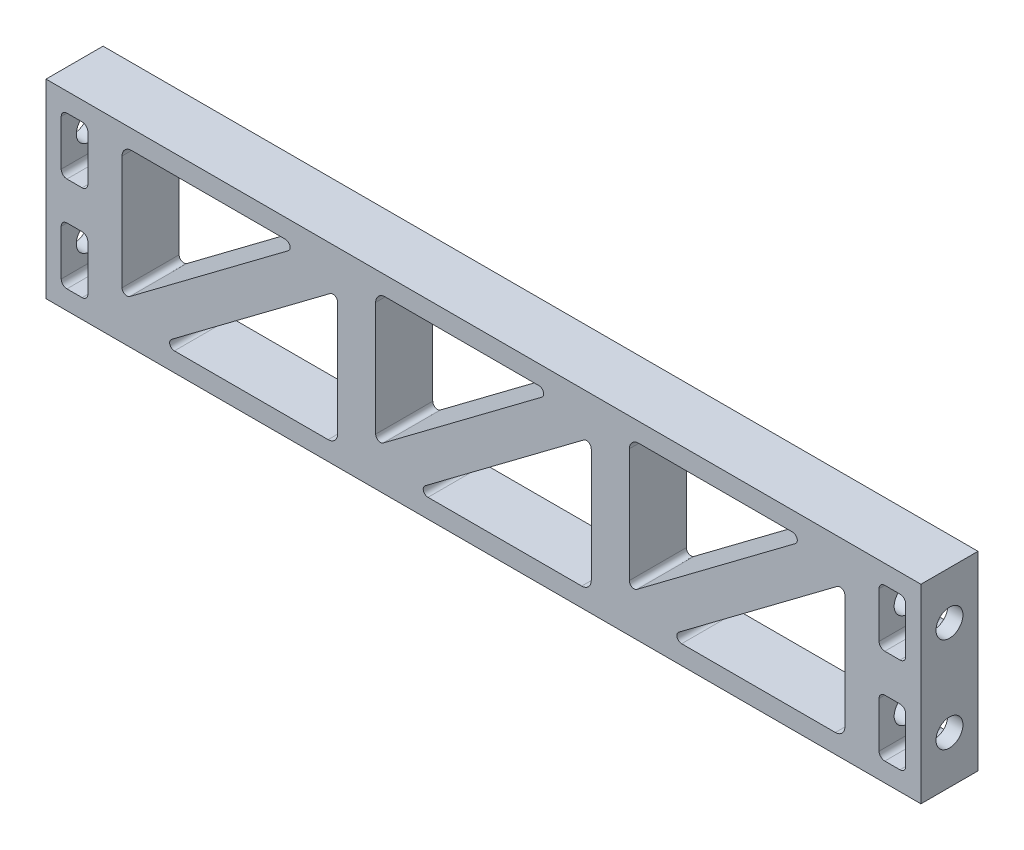
SolidWorks part; units mm, degrees
material "PE High Density"
ref_plane "Front Plane" through (0, 0, 0) normal (0, 0, 1) x (1, 0, 0)
ref_plane "Top Plane" through (0, 0, 0) normal (0, 1, 0) x (1, 0, 0)
ref_plane "Right Plane" through (0, 0, 0) normal (1, 0, 0) x (0, 0, -1)
sketch "Sketch1" plane through (0, 0, 0) normal (0, 0, 1) x (1, 0, 0)
  line L0 (-24.3417, 15.875) -> (-24.3417, -15.875) construction
  line L1 (-73.025, 15.875) -> (73.025, 15.875)
  line L2 (-73.025, 15.875) -> (-73.025, -15.875)
  line L3 (-73.025, -15.875) -> (73.025, -15.875)
  line L4 (73.025, 15.875) -> (73.025, -15.875)
  line L5 (-73.025, 15.875) -> (73.025, -15.875) construction
  line L6 (-73.025, -15.875) -> (73.025, 15.875) construction
  line L7 (24.3417, 15.875) -> (24.3417, -15.875) construction
  line L9 (-69.85, -12.7) -> (-27.5167, 12.7) construction
  line L10 (-69.85, -12.7) -> (-69.85, 12.7) construction
  line L11 (-64.3071, -11.2256) -> (-29.9209, 9.4061)
  line L12 (-73.025, -15.875) -> (-24.3417, -15.875)
  line L13 (-73.025, -15.875) -> (-73.025, 15.875)
  line L14 (-73.025, 15.875) -> (-24.3417, 15.875)
  line L15 (-24.3417, -15.875) -> (-24.3417, 15.875) construction
  line L16 (-69.85, 12.7) -> (-27.5167, 12.7) construction
  line L17 (-27.5167, -12.7) -> (-27.5167, 12.7) construction
  line L18 (-69.85, -12.7) -> (-27.5167, -12.7) construction
  line L19 (-67.4457, -9.4061) -> (-33.0595, 11.2256)
  line L20 (-69.0332, -14.0613) -> (-26.6999, 11.3387) construction
  line L21 (-69.85, -8.0448) -> (-69.85, 11.1125)
  line L22 (-70.6668, -11.3387) -> (-28.3334, 14.0613) construction
  line L23 (-68.2625, 12.7) -> (-33.4679, 12.7)
  line L24 (-63.8988, -12.7) -> (-29.1042, -12.7)
  line L25 (-27.5167, -11.1125) -> (-27.5167, 8.0448)
  line L26 (-15.6238, -11.2256) -> (18.7624, 9.4061)
  line L27 (-18.7624, -9.4061) -> (15.6238, 11.2256)
  line L28 (-21.1667, -8.0448) -> (-21.1667, 11.1125)
  line L29 (-19.5792, 12.7) -> (15.2154, 12.7)
  line L30 (-15.2154, -12.7) -> (19.5792, -12.7)
  line L31 (21.1667, -11.1125) -> (21.1667, 8.0448)
  line L32 (-21.1667, -12.7) -> (21.1667, 12.7) construction
  line L33 (-21.1667, -12.7) -> (-21.1667, 12.7) construction
  line L34 (-21.1667, 12.7) -> (21.1667, 12.7) construction
  line L35 (21.1667, -12.7) -> (21.1667, 12.7) construction
  line L36 (-21.1667, -12.7) -> (21.1667, -12.7) construction
  line L37 (33.0595, -11.2256) -> (67.4457, 9.4061)
  line L38 (29.9209, -9.4061) -> (64.3071, 11.2256)
  line L39 (27.5167, -8.0448) -> (27.5167, 11.1125)
  line L40 (29.1042, 12.7) -> (63.8988, 12.7)
  line L41 (33.4679, -12.7) -> (68.2625, -12.7)
  line L42 (69.85, -11.1125) -> (69.85, 8.0448)
  line L43 (27.5167, -12.7) -> (69.85, 12.7) construction
  line L44 (27.5167, -12.7) -> (27.5167, 12.7) construction
  line L45 (27.5167, 12.7) -> (69.85, 12.7) construction
  line L46 (69.85, -12.7) -> (69.85, 12.7) construction
  line L47 (27.5167, -12.7) -> (69.85, -12.7) construction
  line L59 (-64.3071, -11.2256) -> (-15.6238, -11.2256) construction
  line L60 (-69.85, 15.875) -> (-69.85, -15.875)
  arc A0 (-33.4679, 12.7) -> (-33.0595, 11.2256) centre (-33.4679, 11.9062) cw
  arc A1 (-69.85, -8.0448) -> (-67.4457, -9.4061) centre (-68.2625, -8.0448) ccw
  arc A2 (-69.85, 11.1125) -> (-68.2625, 12.7) centre (-68.2625, 11.1125) cw
  arc A3 (-27.5167, 8.0448) -> (-29.9209, 9.4061) centre (-29.1042, 8.0448) ccw
  arc A4 (-63.8988, -12.7) -> (-64.3071, -11.2256) centre (-63.8988, -11.9062) cw
  arc A5 (-27.5167, -11.1125) -> (-29.1042, -12.7) centre (-29.1042, -11.1125) cw
  arc A6 (15.2154, 12.7) -> (15.6238, 11.2256) centre (15.2154, 11.9062) cw
  arc A7 (-21.1667, -8.0448) -> (-18.7624, -9.4061) centre (-19.5792, -8.0448) ccw
  arc A8 (-21.1667, 11.1125) -> (-19.5792, 12.7) centre (-19.5792, 11.1125) cw
  arc A9 (21.1667, 8.0448) -> (18.7624, 9.4061) centre (19.5792, 8.0448) ccw
  arc A10 (-15.2154, -12.7) -> (-15.6238, -11.2256) centre (-15.2154, -11.9062) cw
  arc A11 (21.1667, -11.1125) -> (19.5792, -12.7) centre (19.5792, -11.1125) cw
  arc A12 (63.8988, 12.7) -> (64.3071, 11.2256) centre (63.8988, 11.9062) cw
  arc A13 (27.5167, -8.0448) -> (29.9209, -9.4061) centre (29.1042, -8.0448) ccw
  arc A14 (27.5167, 11.1125) -> (29.1042, 12.7) centre (29.1042, 11.1125) cw
  arc A15 (69.85, 8.0448) -> (67.4457, 9.4061) centre (68.2625, 8.0448) ccw
  arc A16 (33.4679, -12.7) -> (33.0595, -11.2256) centre (33.4679, -11.9062) cw
  arc A17 (69.85, -11.1125) -> (68.2625, -12.7) centre (68.2625, -11.1125) cw
  point P0 (0, 0)
  point P26 (-30.6022, 12.7)
  point P29 (-69.85, -10.8487)
  point P35 (-27.5167, 10.8487)
  point P38 (-66.7645, -12.7)
  dimension "D7" = 0.7937
  dimension "D8" = 1.5875
  dimension "D9" = 1.5875
  dimension "D10" = 1.5875
  dimension "D11" = 0.7937
  dimension "D12" = 1.5875
  dimension "D1" = 31.75
  dimension "CrossBraceLength" = 146.05
  dimension "D4" = 48.6833
  dimension "D14" = 48.6833
  dimension "D6" = 3.175
  dimension "D2" = 1.5875
  dimension "D5" = 1.5875
  dimension "D3" = 3
  dimension "D13" = 3
extrude "Boss-Extrude1" [suppressed] add sketch "Sketch1" along normal blind 9.525
sketch "Sketch2" plane through (0, 0, 0) normal (0, 0, 1) x (1, 0, 0)
  line L0 (-63.5, 15.875) -> (-63.5, -15.875) construction
  line L1 (-73.025, 15.875) -> (73.025, 15.875)
  line L2 (-73.025, 15.875) -> (-73.025, -15.875)
  line L3 (-73.025, -15.875) -> (73.025, -15.875)
  line L4 (73.025, 15.875) -> (73.025, -15.875)
  line L5 (-73.025, 15.875) -> (73.025, -15.875) construction
  line L6 (-73.025, -15.875) -> (73.025, 15.875) construction
  line L7 (63.5, 15.875) -> (63.5, -15.875) construction
  line L8 (-63.5, -15.875) -> (-63.5, 15.875) construction
  line L9 (-21.1667, -15.875) -> (-21.1667, 15.875) construction
  line L10 (21.1667, -15.875) -> (21.1667, 15.875) construction
  line L11 (-73.025, 0) -> (73.025, 0) construction
  line L12 (-63.5, -15.875) -> (-21.1667, -15.875) construction
  line L13 (-63.5, -15.875) -> (-21.1667, 15.875) construction
  line L14 (-63.5, -15.875) -> (-63.5, 15.875) construction
  line L15 (-63.5, 15.875) -> (-21.1667, 15.875)
  line L16 (-58.7375, 12.7) -> (-33.0729, 12.7)
  line L17 (-59.055, -8.5725) -> (-32.5967, 11.2713)
  line L18 (-60.325, -7.9375) -> (-60.325, 11.1125)
  line L19 (-60.325, 12.7) -> (-30.6917, 12.7) construction
  line L20 (-60.325, -9.525) -> (-30.6917, 12.7) construction
  line L21 (-60.325, -9.525) -> (-60.325, 12.7) construction
  line L22 (-63.5, -15.875) -> (-21.1667, -15.875)
  line L23 (-21.1667, -15.875) -> (-21.1667, 15.875) construction
  line L24 (-51.5938, -12.7) -> (-25.9292, -12.7)
  line L25 (-24.3417, -11.1125) -> (-24.3417, 7.9375)
  line L26 (-52.07, -11.2713) -> (-25.6117, 8.5725)
  line L27 (-53.975, -12.7) -> (-24.3417, 9.525) construction
  line L28 (-24.3417, -12.7) -> (-24.3417, 9.525) construction
  line L29 (-53.975, -12.7) -> (-24.3417, -12.7) construction
  line L30 (17.9917, -11.1125) -> (17.9917, 7.9375)
  line L31 (-9.2604, -12.7) -> (16.4042, -12.7)
  line L32 (-9.7367, -11.2713) -> (16.7217, 8.5725)
  line L33 (-16.7217, -8.5725) -> (9.7367, 11.2713)
  line L34 (-16.4042, 12.7) -> (9.2604, 12.7)
  line L35 (-17.9917, -7.9375) -> (-17.9917, 11.1125)
  line L36 (60.325, -11.1125) -> (60.325, 7.9375)
  line L37 (33.0729, -12.7) -> (58.7375, -12.7)
  line L38 (32.5967, -11.2713) -> (59.055, 8.5725)
  line L39 (25.6117, -8.5725) -> (52.07, 11.2713)
  line L40 (25.9292, 12.7) -> (51.5937, 12.7)
  line L41 (24.3417, -7.9375) -> (24.3417, 11.1125)
  line L48 (-24.3417, -11.1125) -> (17.9917, -11.1125) construction
  line L61 (-69.5325, 12.7) -> (-66.9925, 12.7)
  line L62 (-70.485, 11.7475) -> (-70.485, 4.1275)
  line L63 (-69.5325, 3.175) -> (-66.9925, 3.175)
  line L64 (-66.04, 11.7475) -> (-66.04, 4.1275)
  line L65 (-70.485, 12.7) -> (-66.04, 3.175) construction
  line L66 (-70.485, 3.175) -> (-66.04, 12.7) construction
  line L67 (-68.2625, 15.875) -> (-68.2625, -15.875) construction
  line L68 (-68.2625, 3.175) -> (-68.2625, 11.967) construction
  line L69 (-70.485, 7.9375) -> (-66.04, 7.9375) construction
  line L70 (-70.485, -7.9375) -> (-66.04, -7.9375) construction
  line L71 (-68.2625, -3.175) -> (-68.2625, -11.967) construction
  line L72 (-70.485, -3.175) -> (-66.04, -12.7) construction
  line L73 (-70.485, -12.7) -> (-66.04, -3.175) construction
  line L74 (-66.04, -11.7475) -> (-66.04, -4.1275)
  line L75 (-69.5325, -3.175) -> (-66.9925, -3.175)
  line L76 (-70.485, -11.7475) -> (-70.485, -4.1275)
  line L77 (-69.5325, -12.7) -> (-66.9925, -12.7)
  line L78 (0, -15.875) -> (0, 15.875) construction
  line L79 (70.485, -12.7) -> (66.04, -3.175) construction
  line L80 (70.485, -3.175) -> (66.04, -12.7) construction
  line L81 (68.2625, -3.175) -> (68.2625, -11.967) construction
  line L82 (70.485, -7.9375) -> (66.04, -7.9375) construction
  line L83 (70.485, 7.9375) -> (66.04, 7.9375) construction
  line L84 (68.2625, 3.175) -> (68.2625, 11.967) construction
  line L85 (68.2625, 15.875) -> (68.2625, -15.875) construction
  line L86 (70.485, 3.175) -> (66.04, 12.7) construction
  line L87 (70.485, 12.7) -> (66.04, 3.175) construction
  line L88 (69.5325, -12.7) -> (66.9925, -12.7)
  line L89 (70.485, -11.7475) -> (70.485, -4.1275)
  line L90 (69.5325, -3.175) -> (66.9925, -3.175)
  line L91 (66.04, -11.7475) -> (66.04, -4.1275)
  line L92 (66.04, 11.7475) -> (66.04, 4.1275)
  line L93 (69.5325, 3.175) -> (66.9925, 3.175)
  line L94 (70.485, 11.7475) -> (70.485, 4.1275)
  line L95 (69.5325, 12.7) -> (66.9925, 12.7)
  line L96 (73.025, 15.875) -> (73.025, -15.875)
  arc A0 (-33.0729, 12.7) -> (-32.5967, 11.2713) centre (-33.0729, 11.9063) cw
  arc A1 (-60.325, 11.1125) -> (-58.7375, 12.7) centre (-58.7375, 11.1125) cw
  arc A2 (-60.325, -7.9375) -> (-59.055, -8.5725) centre (-59.5313, -7.9375) ccw
  arc A3 (-25.6117, 8.5725) -> (-24.3417, 7.9375) centre (-25.1354, 7.9375) cw
  arc A4 (-25.9292, -12.7) -> (-24.3417, -11.1125) centre (-25.9292, -11.1125) ccw
  arc A5 (-51.5938, -12.7) -> (-52.07, -11.2713) centre (-51.5938, -11.9063) cw
  arc A6 (16.4042, -12.7) -> (17.9917, -11.1125) centre (16.4042, -11.1125) ccw
  arc A7 (-9.2604, -12.7) -> (-9.7367, -11.2713) centre (-9.2604, -11.9063) cw
  arc A8 (16.7217, 8.5725) -> (17.9917, 7.9375) centre (17.1979, 7.9375) cw
  arc A9 (9.2604, 12.7) -> (9.7367, 11.2713) centre (9.2604, 11.9063) cw
  arc A10 (-17.9917, 11.1125) -> (-16.4042, 12.7) centre (-16.4042, 11.1125) cw
  arc A11 (-17.9917, -7.9375) -> (-16.7217, -8.5725) centre (-17.1979, -7.9375) ccw
  arc A12 (58.7375, -12.7) -> (60.325, -11.1125) centre (58.7375, -11.1125) ccw
  arc A13 (33.0729, -12.7) -> (32.5967, -11.2713) centre (33.0729, -11.9063) cw
  arc A14 (59.055, 8.5725) -> (60.325, 7.9375) centre (59.5312, 7.9375) cw
  arc A15 (51.5937, 12.7) -> (52.07, 11.2713) centre (51.5937, 11.9063) cw
  arc A16 (24.3417, 11.1125) -> (25.9292, 12.7) centre (25.9292, 11.1125) cw
  arc A17 (24.3417, -7.9375) -> (25.6117, -8.5725) centre (25.1354, -7.9375) ccw
  arc A36 (-66.9925, 3.175) -> (-66.04, 4.1275) centre (-66.9925, 4.1275) ccw
  arc A37 (-66.9925, 12.7) -> (-66.04, 11.7475) centre (-66.9925, 11.7475) cw
  arc A38 (-69.5325, 3.175) -> (-70.485, 4.1275) centre (-69.5325, 4.1275) cw
  arc A39 (-69.5325, 12.7) -> (-70.485, 11.7475) centre (-69.5325, 11.7475) ccw
  arc A40 (-69.5325, -12.7) -> (-70.485, -11.7475) centre (-69.5325, -11.7475) cw
  arc A41 (-69.5325, -3.175) -> (-70.485, -4.1275) centre (-69.5325, -4.1275) ccw
  arc A42 (-66.9925, -12.7) -> (-66.04, -11.7475) centre (-66.9925, -11.7475) ccw
  arc A43 (-66.9925, -3.175) -> (-66.04, -4.1275) centre (-66.9925, -4.1275) cw
  arc A44 (66.9925, -3.175) -> (66.04, -4.1275) centre (66.9925, -4.1275) ccw
  arc A45 (66.9925, -12.7) -> (66.04, -11.7475) centre (66.9925, -11.7475) cw
  arc A46 (69.5325, -3.175) -> (70.485, -4.1275) centre (69.5325, -4.1275) cw
  arc A47 (69.5325, -12.7) -> (70.485, -11.7475) centre (69.5325, -11.7475) ccw
  arc A48 (69.5325, 12.7) -> (70.485, 11.7475) centre (69.5325, 11.7475) cw
  arc A49 (69.5325, 3.175) -> (70.485, 4.1275) centre (69.5325, 4.1275) ccw
  arc A50 (66.9925, 12.7) -> (66.04, 11.7475) centre (66.9925, 11.7475) ccw
  arc A51 (66.9925, 3.175) -> (66.04, 4.1275) centre (66.9925, 4.1275) cw
  point P0 (0, 0)
  point P16 (-68.2625, 7.9375)
  point P124 (-68.2625, -7.9375)
  point P168 (68.2625, -7.9375)
  point P169 (68.2625, 7.9375)
  dimension "D9" = 1.5875
  dimension "D8" = 0.7937
  dimension "D10" = 0.7937
  dimension "D12" = 0.7937
  dimension "D13" = 1.5875
  dimension "D14" = 0.7937
  dimension "D19" = 0.9525
  dimension "D20" = 0.9525
  dimension "D21" = 0.9525
  dimension "D22" = 0.9525
  dimension "D1" = 146.05
  dimension "D2" = 31.75
  dimension "D3" = 9.525
  dimension "D4" = 9.525
  dimension "D6" = 42.3333
  dimension "D15" = 42.3333
  dimension "D17" = 4.445
  dimension "D18" = 9.525
  dimension "D23" = 4.7625
  dimension "D24" = 7.9375
  dimension "D7" = 3.175
  dimension "D11" = 3.175
  dimension "D5" = 3
  dimension "D16" = 3
extrude "Boss-Extrude2" add sketch "Sketch2" along normal blind 9.525
sketch "Sketch3" plane through (-73.025, 0, 0) normal (-1, 0, 0) x (0, 0, 1)
  line L0 (9.525, 15.875) -> (0, 15.875) construction
  line L1 (0, 0) -> (9.525, 0) construction
  line L2 (9.525, 15.875) -> (9.525, -15.875) construction
  line L3 (4.7625, -15.875) -> (4.7625, 15.875) construction
  line L4 (9.525, -15.875) -> (0, -15.875) construction
  circle A0 centre (4.7625, 7.9375) radius 2.2479
  dimension "D2" = 4.4958
  dimension "D1" = 7.9375
extrude "Cut-Extrude1" cut sketch "Sketch3" against normal blind 11.1125
mirror "Mirror1" about plane through (0, 0, 0) normal (1, 0, 0) of "Cut-Extrude1" second plane through (0, 0, 0) second plane normal (0, 1, 0)
equation "\"Plate Width\" = 4.6in"
equation "\"Plate Thickness\" = 0.375in"
equation "\"Num holes\" = 4"
equation "\"Plate Height\" = 1.25in"
equation "\"Top Plate Width\" = 4.5in"
equation "\"Plate Clearance Hole Diameter\" = 0.125in"
equation "\"Plate Tap Hole Diameter\" = 0.116in"
equation "\"Bottom Plate Length\" = 6.5in"
equation "\"CrossBraceLength@Sketch1\" = \"Bottom Plate Length\" - 2 * \"Plate Thickness\""
equation "\"D1@Sketch1\"=\"Plate Height\""
equation "\"num_triangle_holes\"= 3"
equation "\"D3@Sketch1\"=\"num_triangle_holes\""
equation "\"D4@Sketch1\"=( \"Bottom Plate Length\" - 2 * \"Plate Thickness\" ) / \"num_triangle_holes\""
equation "\"BorderThickness\"= 0.125"
equation "\"D6@Sketch1\"=\"BorderThickness\""
equation "\"D2@Sketch1\"=\"BorderThickness\"/2"
equation "\"D9@Sketch1\"=\"BorderThickness\"/2"
equation "\"D8@Sketch1\"=\"BorderThickness\"/2"
equation "\"D7@Sketch1\"=\"BorderThickness\"/4"
equation "\"D10@Sketch1\"=\"BorderThickness\"/2"
equation "\"D11@Sketch1\"=\"BorderThickness\"/4"
equation "\"D12@Sketch1\"=\"BorderThickness\"/2"
equation "\"D13@Sketch1\"=\"num_triangle_holes\""
equation "\"D14@Sketch1\"=( \"Bottom Plate Length\" - 2 * \"Plate Thickness\" ) / \"num_triangle_holes\""
equation "\"D1@Boss-Extrude1\"=\"Plate Thickness\""
equation "\"D1@Sketch2\"=\"Bottom Plate Length\" - 2 * \"Plate Thickness\""
equation "\"D2@Sketch2\"=\"Plate Height\""
equation "\"wall_thickness\"= 0.375"
equation "\"D3@Sketch2\"=\"wall_thickness\""
equation "\"D4@Sketch2\"=\"wall_thickness\""
equation "\"D5@Sketch2\"=\"num_triangle_holes\""
equation "\"D6@Sketch2\"=( \"Bottom Plate Length\" - 2 * \"Plate Thickness\" - 2 * \"wall_thickness\" ) / \"num_triangle_holes\" "
equation "\"D7@Sketch2\"=\"BorderThickness\""
equation "\"D8@Sketch2\"=\"BorderThickness\" / 4"
equation "\"D10@Sketch2\"=\"BorderThickness\" / 4"
equation "\"D11@Sketch2\"=\"BorderThickness\""
equation "\"D9@Sketch2\"=\"BorderThickness\"/2"
equation "\"D13@Sketch2\"=\"BorderThickness\"/2"
equation "\"D14@Sketch2\"=\"BorderThickness\"/4"
equation "\"D12@Sketch2\"=\"BorderThickness\"/4"
equation "\"D15@Sketch2\"=( \"Bottom Plate Length\" - 2 * \"Plate Thickness\" - 2 * \"wall_thickness\" ) / \"num_triangle_holes\""
equation "\"D1@Boss-Extrude2\"=\"Plate Thickness\""
equation "\"D16@Sketch2\"=\"num_triangle_holes\""
equation "\"D23@Sketch2\"=\"wall_thickness\"/2"
equation "\"D24@Sketch2\"=\"Plate Height\"/4"
equation "\"Number Eight Clearance Size\" = 0.177in"
equation "\"D1@Sketch3\"=\"Plate Height\" / 4"
equation "\"D2@Sketch3\"=\"Number Eight Clearance Size\""
equation "\"D1@Cut-Extrude1\"=(0.75 - \"Plate Thickness\") + 0.0625"
